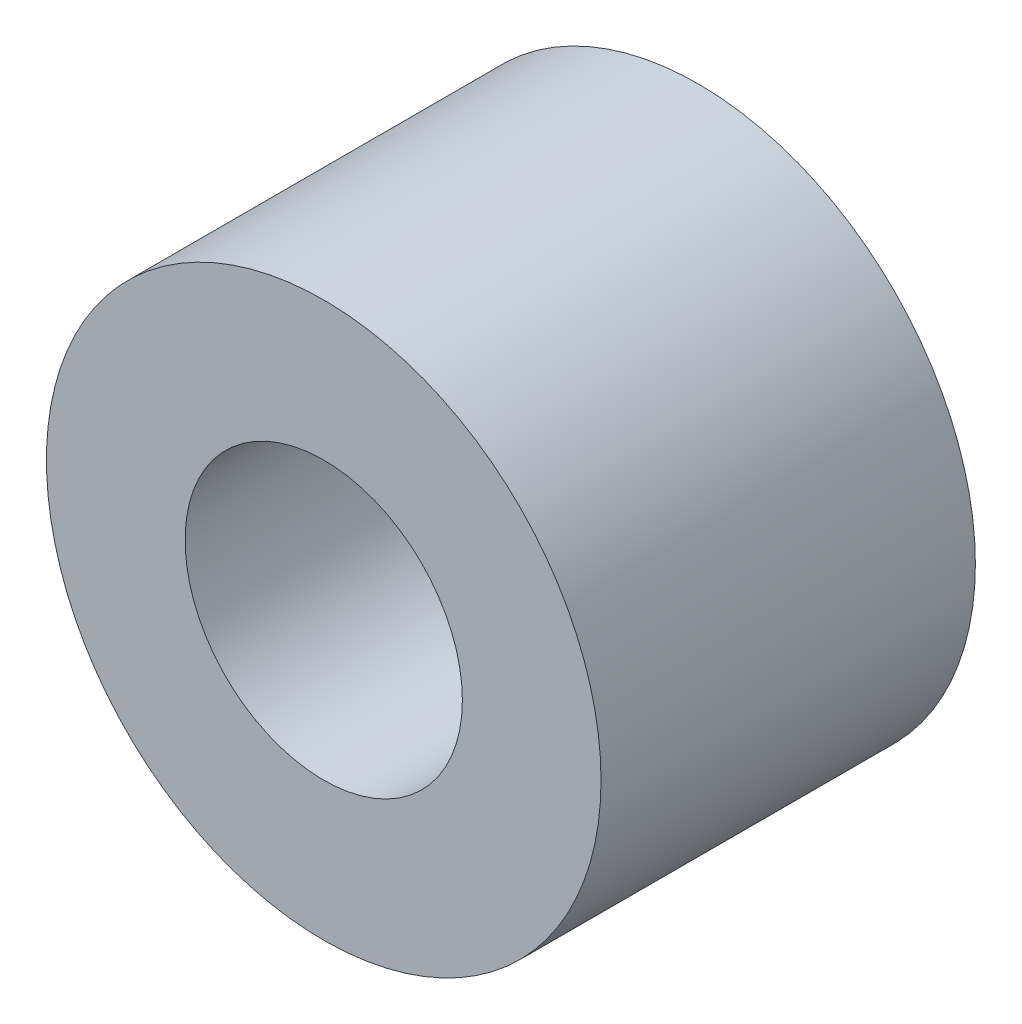
SolidWorks part; units mm, degrees
ref_plane "Alzado" through (0, 0, 0) normal (0, 0, 1) x (1, 0, 0)
ref_plane "Planta" through (0, 0, 0) normal (0, 1, 0) x (1, 0, 0)
ref_plane "Vista lateral" through (0, 0, 0) normal (1, 0, 0) x (0, 0, -1)
sketch "Croquis1" plane through (0, 0, 0) normal (0, 0, 1) x (1, 0, 0)
  circle A0 centre (0, 0) radius 1
  circle A1 centre (0, 0) radius 2
  dimension "D1" = 2
  dimension "D2" = 4
extrude "Saliente-Extruir1" add sketch "Croquis1" along normal blind 2.7
